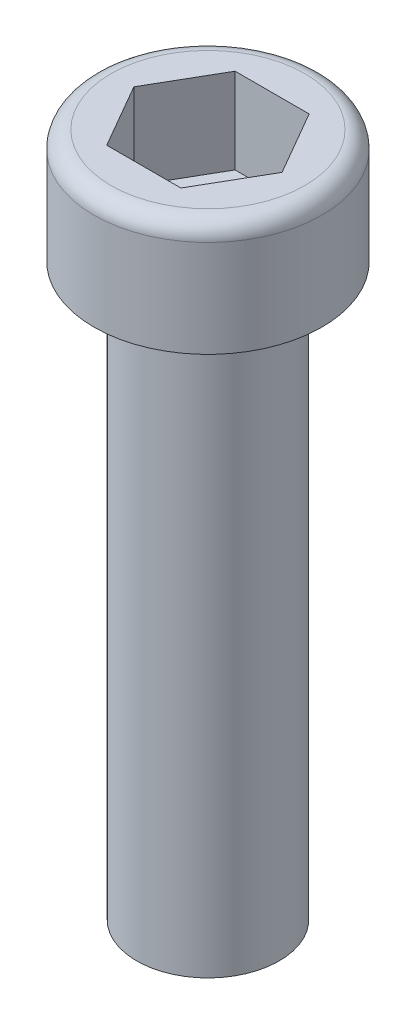
SolidWorks part; units mm, degrees
ref_plane "Front Plane" through (0, 0, 0) normal (0, 0, 1) x (1, 0, 0)
ref_plane "Top Plane" through (0, 0, 0) normal (0, 1, 0) x (1, 0, 0)
ref_plane "Right Plane" through (0, 0, 0) normal (1, 0, 0) x (0, 0, -1)
sketch "Sketch1" plane through (0, 0, 0) normal (0, 1, 0) x (1, 0, 0)
  circle A0 centre (0, 0) radius 2
  dimension "D1" = 4
extrude "Boss-Extrude1" add sketch "Sketch1" along normal blind 2
sketch "Sketch2" plane through (0, 0, 0) normal (0, -1, 0) x (1, 0, 0)
  circle A0 centre (0, 0) radius 1.25
  dimension "D1" = 2.5
extrude "Boss-Extrude2" add sketch "Sketch2" along normal blind 10
fillet "Fillet1" radius 0.3 1 edges at (0, 2, 2)
sketch "Sketch4" plane through (0, 2, 0) normal (0, 1, 0) x (1, 0, 0)
  line L1 (1.299, 0) -> (0.6495, 1.125)
  line L2 (0.6495, 1.125) -> (-0.6495, 1.125)
  line L3 (-0.6495, 1.125) -> (-1.299, 0)
  line L4 (-1.299, 0) -> (-0.6495, -1.125)
  line L5 (-0.6495, -1.125) -> (0.6495, -1.125)
  line L6 (0.6495, -1.125) -> (1.299, 0)
  circle A0 centre (0, 0) radius 1.125 construction
  dimension "D1" = 2.25
extrude "Cut-Extrude1" cut sketch "Sketch4" against normal blind 1.5
